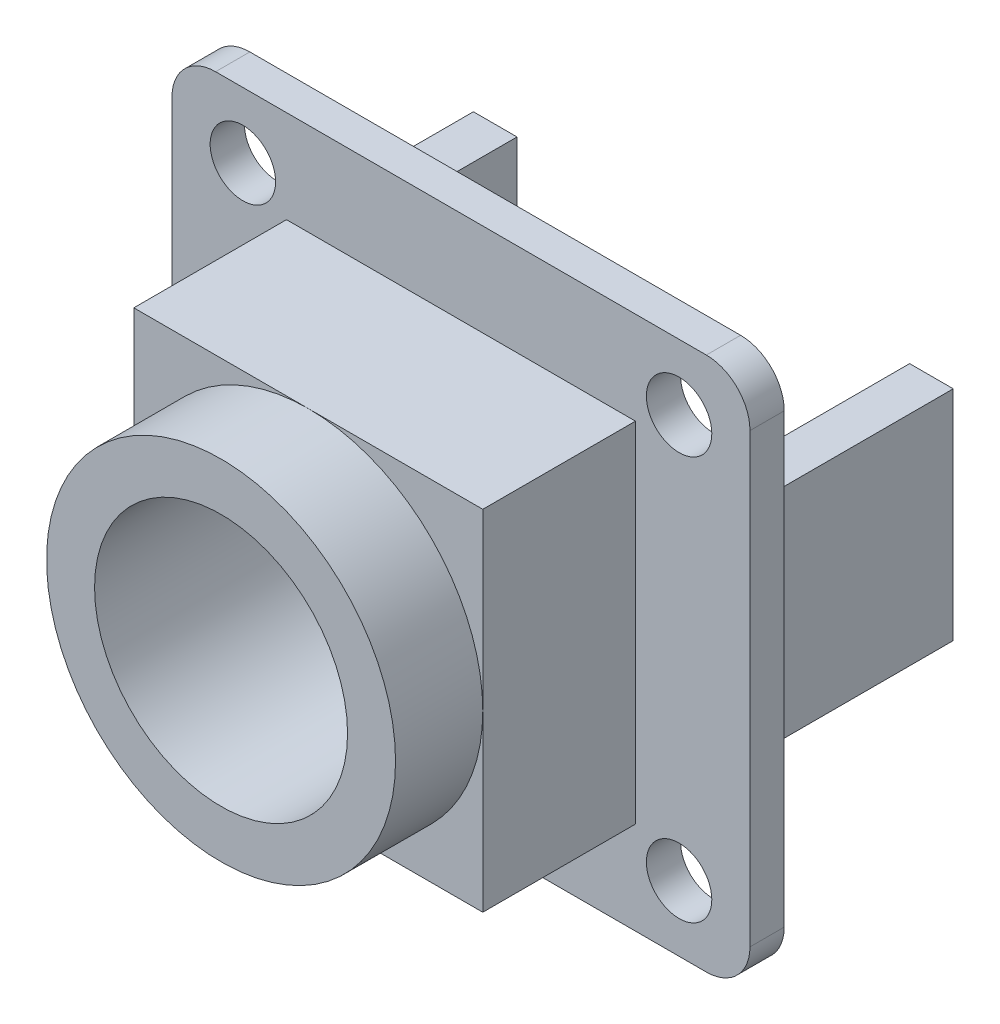
SolidWorks part; units mm, degrees
ref_plane "前视基准面" through (0, 0, 0) normal (0, 0, 1) x (1, 0, 0)
ref_plane "上视基准面" through (0, 0, 0) normal (0, 1, 0) x (1, 0, 0)
ref_plane "右视基准面" through (0, 0, 0) normal (1, 0, 0) x (0, 0, -1)
sketch "草图1" plane through (0, 0, 0) normal (0, 0, 1) x (1, 0, 0)
  line L1 (-13.25, 12.25) -> (13.25, 12.25)
  line L2 (-13.25, 12.25) -> (-13.25, -12.25)
  line L3 (-13.25, -12.25) -> (13.25, -12.25)
  line L4 (13.25, 12.25) -> (13.25, -12.25)
  line L5 (0, -12.25) -> (0, 12.25) construction
  line L6 (-13.25, 0) -> (13.25, 0) construction
  line L7 (-10, 9.25) -> (10, 9.25) construction
  line L8 (-10, 9.25) -> (-10, -9.25) construction
  line L9 (-10, -9.25) -> (10, -9.25) construction
  line L10 (10, 9.25) -> (10, -9.25) construction
  line L11 (0, -9.25) -> (0, 9.25) construction
  line L12 (-10, 0) -> (10, 0) construction
  circle A0 centre (-10, 9.25) radius 1.5
  circle A1 centre (10, 9.25) radius 1.5
  circle A2 centre (10, -9.25) radius 1.5
  circle A3 centre (-10, -9.25) radius 1.5
  point P0 (0, 0)
  point P4 (0, 0)
  dimension "D3" = 3
  dimension "D1" = 26.5
  dimension "D2" = 24.5
  dimension "D4" = 20
  dimension "D5" = 18.5
extrude "凸台-拉伸1" add sketch "草图1" along normal blind 1.57
ref_plane "基准面4" through (0, 0, 12.57) normal (0, 0, 1) x (1, 0, 0)
sketch "草图3" plane through (0, 0, 1.57) normal (0, 0, 1) x (1, 0, 0)
  line L1 (8, -8) -> (8, 8)
  line L2 (8, 8) -> (-8, 8)
  line L3 (-8, 8) -> (-8, -8)
  line L4 (-8, -8) -> (8, -8)
  circle A0 centre (0, 0) radius 8 construction
  dimension "D1" = 16
extrude "凸台-拉伸2" add sketch "草图3" along normal blind 7
sketch "草图4" plane through (0, 0, 8.57) normal (0, 0, 1) x (1, 0, 0)
  circle A0 centre (0, 0) radius 8
  dimension "D1" = 16
extrude "凸台-拉伸3" add sketch "草图4" along normal up to surface (4 mm away) up to plane "基准面4"
sketch "草图5" plane through (0, 0, 12.57) normal (0, 0, 1) x (1, 0, 0)
  circle A0 centre (0, 0) radius 5.8
  dimension "D1" = 11.6
extrude "切除-拉伸1" cut sketch "草图5" against normal up to surface (11 mm away) up to face at (11.5, -9.25, 1.57)
fillet "圆角1" radius 2 4 edges at (13.25, -12.25, 0.785) (13.25, 12.25, 0.785) (-13.25, -12.25, 0.785) (-13.25, 12.25, 0.785)
sketch "草图6" plane through (0, 0, 0) normal (0, 0, -1) x (-1, 0, 0)
  line L0 (0, 6.9135) -> (0, -6.9135) construction
  line L1 (-11, 5) -> (-9, 5)
  line L2 (-11, 5) -> (-11, -5)
  line L3 (-11, -5) -> (-9, -5)
  line L4 (-9, 5) -> (-9, -5)
  line L5 (9, 5) -> (9, -5)
  line L6 (11, -5) -> (9, -5)
  line L7 (11, 5) -> (11, -5)
  line L8 (11, 5) -> (9, 5)
  circle A5 centre (-10, 9.25) radius 1.5 construction
  circle A6 centre (-10, 9.25) radius 1.5
  point P7 (-10, 5)
  point P8 (-9, 0)
  dimension "D1" = 10
  dimension "D2" = 2
extrude "凸台-拉伸4" add sketch "草图6" along normal blind 10 contours L4 L1 L2 L3 | L7 L8 L5 L6
